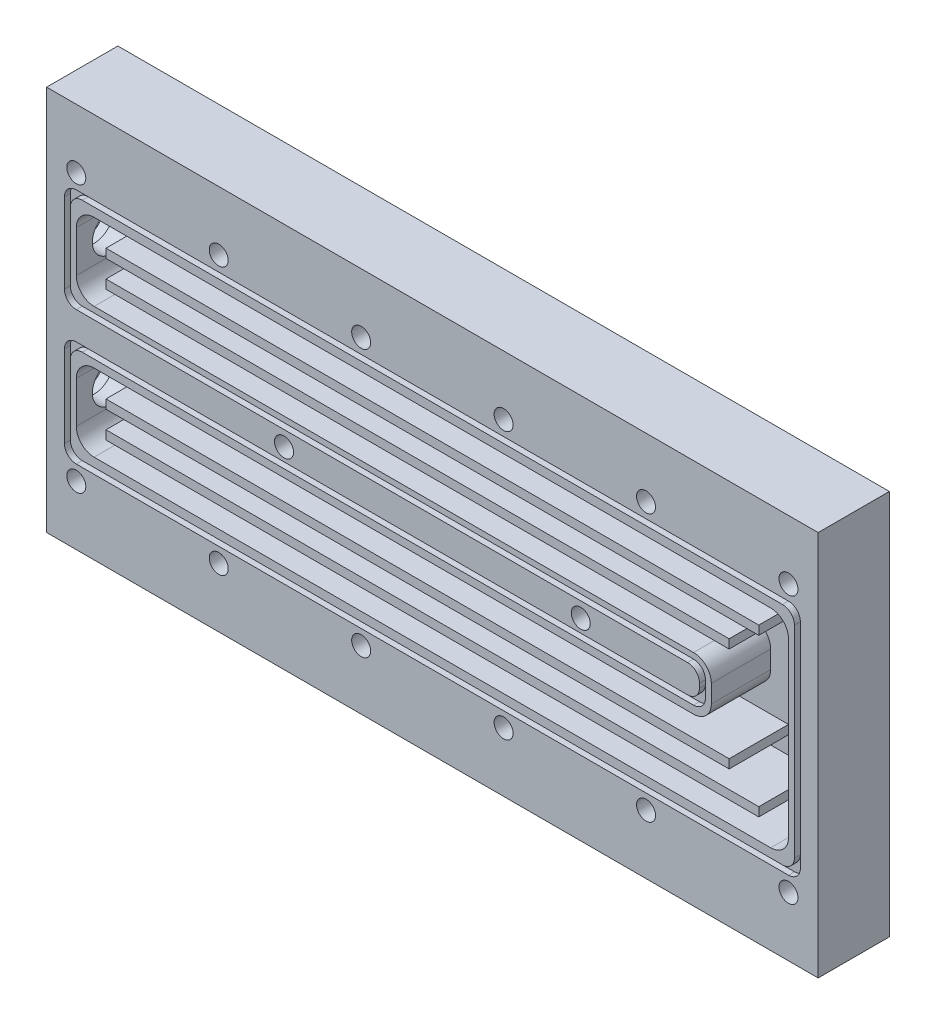
SolidWorks part; units mm, degrees
ref_plane "Plan de face" through (0, 0, 0) normal (0, 0, 1) x (1, 0, 0)
ref_plane "Plan de dessus" through (0, 0, 0) normal (0, 1, 0) x (1, 0, 0)
ref_plane "Plan de droite" through (0, 0, 0) normal (1, 0, 0) x (0, 0, -1)
sketch "Esquisse1" plane through (0, 0, 0) normal (0, 0, 1) x (1, 0, 0)
  line L1 (0, 0) -> (130, 0)
  line L2 (0, 0) -> (0, 65)
  line L3 (0, 65) -> (130, 65)
  line L4 (130, 0) -> (130, 65)
  dimension "D1" = 130
  dimension "D2" = 65
extrude "Boss.-Extru.1" add sketch "Esquisse1" along normal blind 12
sketch "Esquisse2" plane through (0, 0, 12) normal (0, 0, 1) x (1, 0, 0)
  line L0 (-5.5409, 55) -> (136.6271, 55) construction
  line L1 (-5.5409, 10) -> (135.6371, 10) construction
  line L2 (130, 65) -> (0, 65) construction
  line L3 (0, 0) -> (130, 0) construction
  line L4 (0, 65) -> (0, 0) construction
  line L5 (130, 0) -> (130, 65) construction
  circle A0 centre (5, 55) radius 1.6
  circle A1 centre (29, 55) radius 1.6
  circle A2 centre (53, 55) radius 1.6
  circle A3 centre (77, 55) radius 1.6
  circle A4 centre (101, 55) radius 1.6
  circle A5 centre (125, 55) radius 1.6
  circle A6 centre (5, 10) radius 1.6
  circle A7 centre (29, 10) radius 1.6
  circle A8 centre (53, 10) radius 1.6
  circle A9 centre (77, 10) radius 1.6
  circle A10 centre (101, 10) radius 1.6
  circle A11 centre (125, 10) radius 1.6
  circle A12 centre (90, 32.5) radius 1.6
  circle A13 centre (40, 32.5) radius 1.6
  dimension "D3" = 5
  dimension "D9" = 50
  dimension "D1" = 10
  dimension "D2" = 10
  dimension "D4" = 24
  dimension "D5" = 24
  dimension "D6" = 24
  dimension "D7" = 24
  dimension "D8" = 24
  dimension "D10" = 40
  dimension "D11" = 32.5
  dimension "D12" = 32.5
extrude "Enlèv. mat.-Extru.1" cut sketch "Esquisse2" against normal through all
sketch "Esquisse6" plane through (0, 0, 12) normal (0, 0, 1) x (1, 0, 0)
  line L0 (8, 50) -> (122, 50)
  line L1 (125, 47) -> (125, 18)
  line L2 (122, 15) -> (8, 15)
  line L3 (5, 18) -> (5, 25)
  line L4 (8, 28) -> (109, 28)
  line L5 (112, 31) -> (112, 34)
  line L6 (109, 37) -> (8, 37)
  line L7 (5, 40) -> (5, 47)
  line L8 (130, 0) -> (130, 65) construction
  line L9 (0, 0) -> (130, 0) construction
  line L10 (130, 65) -> (0, 65) construction
  line L11 (0, 65) -> (0, 0) construction
  arc A0 (122, 50) -> (125, 47) centre (122, 47) cw
  arc A1 (112, 34) -> (109, 37) centre (109, 34) ccw
  arc A2 (109, 28) -> (112, 31) centre (109, 31) ccw
  arc A3 (125, 18) -> (122, 15) centre (122, 18) cw
  arc A4 (8, 15) -> (5, 18) centre (8, 18) cw
  arc A5 (5, 25) -> (8, 28) centre (8, 25) cw
  arc A6 (8, 37) -> (5, 40) centre (8, 40) cw
  arc A7 (8, 50) -> (5, 47) centre (8, 47) ccw
  dimension "D9" = 3
  dimension "D1" = 5
  dimension "D2" = 13
  dimension "D3" = 15
  dimension "D4" = 13
  dimension "D5" = 15
  dimension "D6" = 13
  dimension "D7" = 5
  dimension "D8" = 5
extrude "Enlèv. mat.-Extru.6" cut sketch "Esquisse6" against normal blind 10
sketch "Esquisse7" plane through (0, 0, 0) normal (-1, 0, 0) x (0, 0, 1)
  line L0 (12, 65) -> (12, 0) construction
  line L1 (12, 0) -> (0, 0) construction
  line L2 (12, 65) -> (0, 65) construction
  circle A0 centre (6, 43.5) radius 2.7
  circle A1 centre (6, 21.5) radius 2.7
  dimension "D1" = 6
  dimension "D2" = 6
  dimension "D3" = 21.5
  dimension "D4" = 21.5
hole_wizard "Dégagement M61" positions "Esquisse8" profile "Esquisse9" hole size "M6" standard "ISO"
sketch "Esquisse8" plane through (0, 0, 0) normal (-1, 0, 0) x (0, 0, 1)
  point P0 (6, 43.5)
  point P3 (6, 21.5)
sketch "Esquisse9" plane through (0, 43.5, 6) normal (0, 1, 0) x (0, 0, 1)
  line L0 (0, 0) -> (0, 8)
  line L1 (0, 8) -> (3.3, 6.0172)
  line L2 (3.3, 6.0172) -> (3.3, 0)
  line L5 (3.3, 0) -> (0, 0)
  line L10 (0, 8) -> (-3.3, 6.0172) construction
  line L11 (0, -6.35) -> (0, 107.95) construction
  dimension "Diamètre du perçage" = 6.6
  dimension "Profondeur du perçage" = 8
  dimension "Angle de pointe" = 118
sketch "Esquisse10" plane through (0, 0, 0) normal (-1, 0, 0) x (0, 0, 1)
  circle A0 centre (6, 21.5) radius 4
  circle A1 centre (6, 43.5) radius 4
extrude "Enlèv. mat.-Extru.7" cut sketch "Esquisse10" against normal blind 2
sketch "Esquisse11" plane through (0, 0, 12) normal (0, 0, 1) x (1, 0, 0)
  line L0 (130, 65) -> (0, 65) construction
  line L1 (6, 51.5) -> (124, 51.5)
  line L3 (6, 13.5) -> (124, 13.5)
  line L4 (126, 49.5) -> (126, 15.5)
  line L5 (125, 12.5) -> (5, 12.5)
  line L6 (127, 14.5) -> (127, 50.5)
  line L7 (125, 52.5) -> (5, 52.5)
  line L9 (0, 0) -> (130, 0) construction
  line L10 (130, 0) -> (130, 65) construction
  line L12 (4, 15.5) -> (4, 27.3158)
  line L13 (6, 29.3158) -> (109, 29.3158)
  line L14 (111, 31.3158) -> (111, 34.0342)
  line L15 (109, 36.0342) -> (6, 36.0342)
  line L16 (4, 38.0342) -> (4, 49.5)
  line L19 (112, 34) -> (112, 31) construction
  line L21 (3, 14.5) -> (3, 28.3158)
  line L22 (5, 30.3158) -> (108, 30.3158)
  line L23 (110, 32.3158) -> (110, 33.0342)
  line L24 (108, 35.0342) -> (5, 35.0342)
  line L25 (3, 37.0342) -> (3, 50.5)
  arc A0 (127, 50.5) -> (125, 52.5) centre (125, 50.5) ccw
  arc A1 (124, 51.5) -> (126, 49.5) centre (124, 49.5) cw
  arc A2 (125, 12.5) -> (127, 14.5) centre (125, 14.5) ccw
  arc A3 (124, 13.5) -> (126, 15.5) centre (124, 15.5) ccw
  arc A4 (4, 15.5) -> (6, 13.5) centre (6, 15.5) ccw
  arc A5 (5, 12.5) -> (3, 14.5) centre (5, 14.5) cw
  arc A6 (5, 52.5) -> (3, 50.5) centre (5, 50.5) ccw
  arc A7 (6, 51.5) -> (4, 49.5) centre (6, 49.5) ccw
  arc A8 (111, 34.0342) -> (109, 36.0342) centre (109, 34.0342) ccw
  arc A9 (109, 29.3158) -> (111, 31.3158) centre (109, 31.3158) ccw
  arc A10 (4, 27.3158) -> (6, 29.3158) centre (6, 27.3158) cw
  arc A11 (6, 36.0342) -> (4, 38.0342) centre (6, 38.0342) cw
  arc A12 (110, 33.0342) -> (108, 35.0342) centre (108, 33.0342) ccw
  arc A13 (108, 30.3158) -> (110, 32.3158) centre (108, 32.3158) ccw
  arc A14 (3, 28.3158) -> (5, 30.3158) centre (5, 28.3158) cw
  arc A15 (5, 35.0342) -> (3, 37.0342) centre (5, 37.0342) cw
  dimension "D1" = 2
  dimension "D3" = 2
  dimension "D9" = 2
  dimension "D2" = 1
  dimension "D4" = 1
  dimension "D5" = 1
  dimension "D6" = 12.5
  dimension "D7" = 12.5
  dimension "D8" = 3
  dimension "D10" = 1
  dimension "D11" = 1
  dimension "D12" = 1
  dimension "D13" = 1
  dimension "D14" = 1
  dimension "D15" = 1
extrude "Enlèv. mat.-Extru.9" cut sketch "Esquisse11" against normal blind 1
sketch "Esquisse12" plane through (0, 0, 2) normal (0, 0, 1) x (1, 0, 0)
  line L0 (109, 28) -> (8, 28) construction
  line L1 (10, 40.5) -> (115, 40.5)
  line L2 (10, 40.5) -> (10, 42)
  line L3 (10, 42) -> (115, 42)
  line L4 (115, 40.5) -> (115, 42)
  line L5 (10, 46.5) -> (120, 46.5)
  line L6 (10, 46.5) -> (10, 45)
  line L7 (10, 45) -> (120, 45)
  line L8 (120, 46.5) -> (120, 45)
  line L9 (10, 18.5) -> (120, 18.5)
  line L10 (10, 18.5) -> (10, 20)
  line L11 (10, 20) -> (120, 20)
  line L12 (120, 18.5) -> (120, 20)
  line L13 (10, 24.5) -> (115, 24.5)
  line L14 (10, 24.5) -> (10, 23)
  line L15 (10, 23) -> (115, 23)
  line L16 (115, 24.5) -> (115, 23)
  line L17 (8, 37) -> (109, 37) construction
  line L18 (122, 50) -> (8, 50) construction
  line L19 (8, 15) -> (122, 15) construction
  line L20 (5, 25) -> (5, 18) construction
  line L21 (5, 47) -> (5, 40) construction
  dimension "D1" = 1.5
  dimension "D2" = 1.5
  dimension "D3" = 110
  dimension "D4" = 105
  dimension "D5" = 105
  dimension "D6" = 110
  dimension "D7" = 1.5
  dimension "D8" = 1.5
  dimension "D9" = 3
  dimension "D10" = 3
  dimension "D11" = 3.5
  dimension "D12" = 3.5
  dimension "D13" = 3.5
  dimension "D14" = 3.5
  dimension "D15" = 5
  dimension "D16" = 5
  dimension "D17" = 5
  dimension "D18" = 5
extrude "Boss.-Extru.2" add sketch "Esquisse12" along normal blind 10
